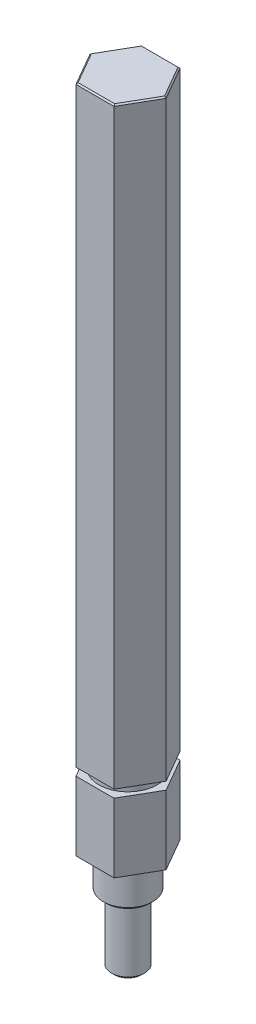
SolidWorks part; units mm, degrees
ref_plane "Front Plane" through (0, 0, 0) normal (0, 0, 1) x (1, 0, 0)
ref_plane "Top Plane" through (0, 0, 0) normal (0, 1, 0) x (1, 0, 0)
ref_plane "Right Plane" through (0, 0, 0) normal (1, 0, 0) x (0, 0, -1)
ref_plane "Plane1" through (0, -25.4, 0) normal (0, -1, 0) x (1, 0, 0)
sketch "Sketch1" plane through (0, -25.4, 0) normal (0, -1, 0) x (1, 0, 0)
  line L0 (-45.6395, -16.669) -> (-41.9733, -23.019)
  line L1 (-41.9733, -23.019) -> (-34.641, -23.019)
  line L2 (-34.641, -23.019) -> (-30.9748, -16.669)
  line L3 (-30.9748, -16.669) -> (-34.641, -10.319)
  line L4 (-34.641, -10.319) -> (-41.9733, -10.319)
  line L5 (-41.9733, -10.319) -> (-45.6395, -16.669)
extrude "Boss-Extrude1" add sketch "Sketch1" against normal blind 13.2842
sketch "Sketch2" plane through (0, -12.1158, 0) normal (0, 1, 0) x (-1, 0, 0)
  circle A0 centre (38.3071, -16.669) radius 5.588
extrude "Boss-Extrude2" add sketch "Sketch2" along normal blind 1.4986
ref_plane "Plane2" through (0, -10.6172, 0) normal (0, -1, 0) x (1, 0, 0)
sketch "Sketch3" plane through (0, -10.6172, 0) normal (0, -1, 0) x (1, 0, 0)
  line L0 (-45.6395, -16.669) -> (-41.9733, -23.019)
  line L1 (-41.9733, -23.019) -> (-34.641, -23.019)
  line L2 (-34.641, -23.019) -> (-30.9748, -16.669)
  line L3 (-30.9748, -16.669) -> (-34.641, -10.319)
  line L4 (-34.641, -10.319) -> (-41.9733, -10.319)
  line L5 (-41.9733, -10.319) -> (-45.6395, -16.669)
extrude "Boss-Extrude3" add sketch "Sketch3" against normal blind 114.0485
ref_plane "Plane3" through (0, 0, -16.669) normal (0, 0, -1) x (-1, 0, 0)
sketch "Sketch4" plane through (0, 0, -16.669) normal (0, 0, -1) x (-1, 0, 0)
  line L0 (35.1448, -45.212) -> (38.3071, -45.212)
  line L1 (38.3071, -45.212) -> (38.3071, -25.4)
  line L2 (38.3071, -25.4) -> (33.5573, -25.4)
  line L3 (33.5573, -25.4) -> (33.5573, -32.512)
  line L4 (33.5573, -32.512) -> (35.1448, -32.512)
  line L5 (35.1448, -32.512) -> (35.1448, -45.212)
  line L6 (38.3071, -45.212) -> (38.3071, -25.4) construction
revolve "Revolve1" add sketch "Sketch4" angle 360 about L6
chamfer "Chamfer1" distance 0.508 angle 45 2 edges at (-38.3071, -32.512, -11.9192) (-38.3071, -45.212, -13.5067)
chamfer "Chamfer2" distance 0.254 angle 45 6 edges at (-32.8079, 103.4313, -13.494) (-32.8079, 103.4313, -19.844) (-38.3071, 103.4313, -10.319) (-38.3071, 103.4313, -23.019) (-43.8064, 103.4313, -13.494) (-43.8064, 103.4313, -19.844)
